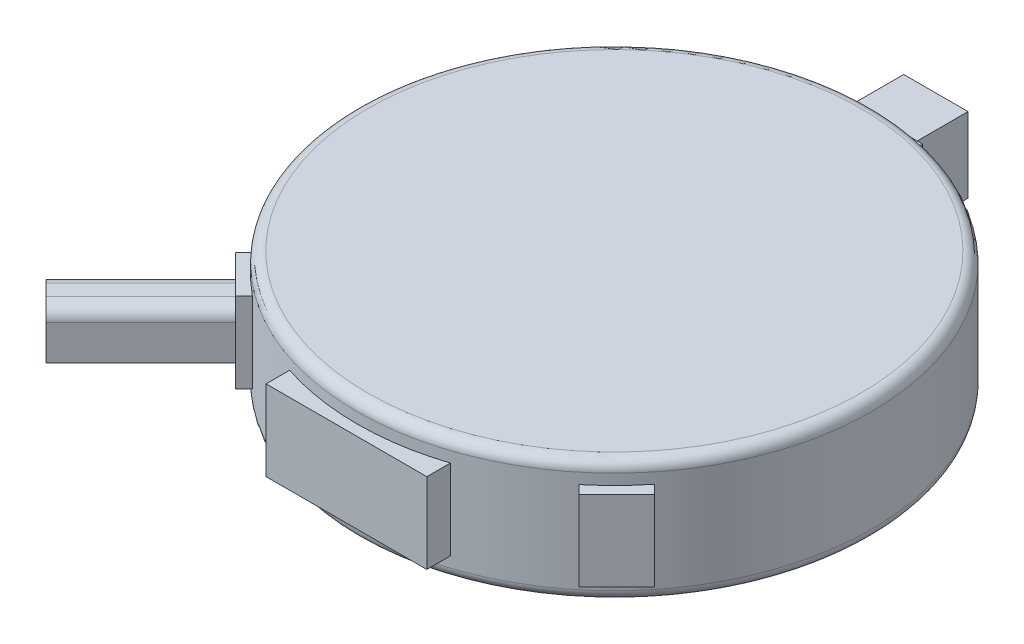
SolidWorks part; units mm, degrees
ref_plane "Face" through (0, 0, 0) normal (0, 0, 1) x (1, 0, 0)
ref_plane "Dessus" through (0, 0, 0) normal (0, 1, 0) x (1, 0, 0)
ref_plane "Droite" through (0, 0, 0) normal (1, 0, 0) x (0, 0, -1)
sketch "Esquisse1" plane through (0, 0, 0) normal (0, 1, 0) x (1, 0, 0)
  line L0 (0, 0) -> (0, 100) construction
  line L1 (-7.5, 100) -> (7.5, 100)
  line L2 (-7.5, 100) -> (-7.5, 50)
  line L3 (-7.5, 50) -> (-39.1047, 18.3953)
  line L4 (-39.1047, 18.3953) -> (-32.0336, 11.3242)
  line L5 (-32.0336, 11.3242) -> (-15, 28.3579)
  line L6 (-15, 28.3579) -> (-15, 0)
  line L7 (-15, 0) -> (15, 0)
  line L8 (15, 0) -> (15, 28.3579)
  line L9 (15, 28.3579) -> (32.0336, 11.3242)
  line L10 (32.0336, 11.3242) -> (39.1047, 18.3953)
  line L11 (39.1047, 18.3953) -> (7.5, 50)
  line L12 (7.5, 50) -> (7.5, 100)
  line L13 (-7.5, 50) -> (7.5, 50) construction
  point P5 (0, 50)
  point P6 (-35.5692, 14.8598)
  point P17 (35.5692, 14.8598)
  point P20 (0, 0)
  dimension "D1" = 50
  dimension "D2" = 15
  dimension "D3" = 50
  dimension "D4" = 50
  dimension "D5" = 45
  dimension "D6" = 30
  dimension "D7" = 10
extrude "Extrusion1" add sketch "Esquisse1" along normal blind 15
sketch "Esquisse2" plane through (0, 15, 0) normal (0, 1, 0) x (1, 0, 0)
  line L0 (-7.5, 50) -> (7.5, 50) construction
  circle A0 centre (0, 50) radius 48
  dimension "D1" = 96
extrude "Extrusion2" add sketch "Esquisse2" along normal blind 4 and the other way blind 19
fillet "Congé1" radius 2 2 edges at (0, -4, -2) (0, 19, -2)
sketch "Esquisse5" plane through (-10.3547, 0, 10.3547) normal (-0.7071, 0, 0.7071) x (0.7071, 0, 0.7071)
  line L0 (-35.6586, 15) -> (-35.6586, 0) construction
  line L1 (-40.6586, 15) -> (-30.6586, 15) construction
  line L2 (-40.6586, 0) -> (-30.6586, 0) construction
  line L3 (-40.6586, 7.5) -> (-30.6586, 7.5) construction
  line L4 (-40.6586, 15) -> (-40.6586, 0) construction
  line L5 (-30.6586, 15) -> (-30.6586, 0) construction
  line L6 (-39.6586, 3.5) -> (-39.6586, 10)
  line L7 (-37.1586, 12.5) -> (-34.1586, 12.5)
  line L8 (-39.6586, 3.5) -> (-31.6586, 3.5)
  line L9 (-37.6586, 10) -> (-37.6586, 5.5)
  line L10 (-37.1586, 10.5) -> (-34.1586, 10.5)
  line L11 (-33.6586, 10) -> (-33.6586, 5.5)
  line L12 (-37.6586, 5.5) -> (-33.6586, 5.5)
  line L13 (-31.6586, 3.5) -> (-31.6586, 10)
  arc A0 (-39.6586, 10) -> (-37.1586, 12.5) centre (-37.1586, 10) cw
  arc A1 (-37.6586, 10) -> (-37.1586, 10.5) centre (-37.1586, 10) cw
  arc A2 (-33.6586, 10) -> (-34.1586, 10.5) centre (-34.1586, 10) ccw
  arc A3 (-31.6586, 10) -> (-34.1586, 12.5) centre (-34.1586, 10) ccw
  point P25 (-35.6586, 10.5)
  point P28 (-35.6586, 12.5)
  point P30 (-35.6586, 5.5)
  point P31 (-35.6586, 3.5)
  dimension "D6" = 2.5
  dimension "D1" = 2
  dimension "D2" = 2
  dimension "D3" = 9
  dimension "D4" = 4
  dimension "D5" = 1
extrude "Extrusion5" add sketch "Esquisse5" along normal blind 25
sketch "Esquisse6" plane through (0, 0, -100) normal (0, 0, -1) x (-1, 0, 0)
  line L0 (0, 15) -> (0, 0) construction
  line L1 (7.5, 15) -> (-7.5, 15) construction
  line L2 (-7.5, 7.5) -> (7.5, 7.5) construction
  line L3 (-7.5, 15) -> (-7.5, 0) construction
  line L4 (7.5, 15) -> (7.5, 0) construction
  line L5 (6, 14.5) -> (-6, 14.5)
  line L6 (-6, 14.5) -> (-6, 0.5)
  line L7 (-5, 1.5) -> (-5, 13.5)
  line L8 (-5, 13.5) -> (5, 13.5)
  line L9 (5, 1.5) -> (5, 13.5)
  line L10 (6, 14.5) -> (6, 0.5)
  line L11 (6, 0.5) -> (-6, 0.5)
  line L12 (-5, 1.5) -> (5, 1.5)
  point P11 (0, 13.5)
  point P14 (-6, 7.5)
  point P21 (0, 14.5)
  point P22 (5, 7.5)
  point P23 (6, 7.5)
  point P25 (-5, 7.5)
  dimension "D1" = 6
  dimension "D2" = 7
  dimension "D3" = 1
  dimension "D4" = 1
extrude "Extrusion6" add sketch "Esquisse6" along normal blind 10
